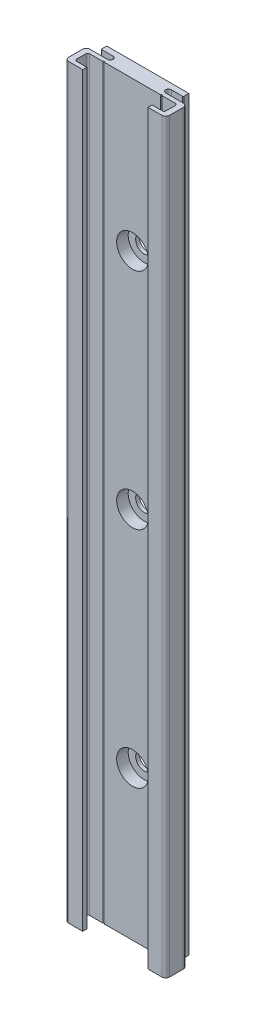
SolidWorks part; units mm, degrees
ref_plane "Plan de face" through (0, 0, 0) normal (0, 0, 1) x (1, 0, 0)
ref_plane "Plan de dessus" through (0, 0, 0) normal (0, 1, 0) x (1, 0, 0)
ref_plane "Plan de droite" through (0, 0, 0) normal (1, 0, 0) x (0, 0, -1)
ref_plane "Plan1" through (0, -100, 0) normal (0, -1, 0) x (1, 0, 0)
sketch "Esquisse1" plane through (0, -100, 0) normal (0, -1, 0) x (1, 0, 0)
  line L0 (-11, 0) -> (11, 0)
  line L1 (11, 0) -> (11, 1.5)
  line L2 (11, 1.5) -> (7.8, 1.5)
  line L3 (7.8, 3) -> (13.5, 3)
  line L4 (13.5, 3) -> (13.5, 8.7)
  line L5 (13.5, 8.7) -> (-13.5, 8.7)
  line L6 (-13.5, 8.7) -> (-13.5, 3)
  line L7 (-13.5, 3) -> (-7.8, 3)
  line L8 (-7.8, 1.5) -> (-11, 1.5)
  line L9 (-11, 1.5) -> (-11, 0)
  arc A0 (7.8, 1.5) -> (7.8, 3) centre (7.8, 2.25) cw
  arc A1 (-7.8, 3) -> (-7.8, 1.5) centre (-7.8, 2.25) cw
extrude "Boss.-Extru.1" add sketch "Esquisse1" against normal blind 200
sketch "Esquisse2" plane through (0, 100, 0) normal (0, 1, 0) x (-1, 0, 0)
  line L0 (8.75, 8.7) -> (-8.75, 8.7)
  line L1 (-8.75, 8.7) -> (-8.75, 7.6)
  line L2 (-8.75, 7.6) -> (-12, 7.6)
  line L3 (-12, 7.6) -> (-12, 4.1)
  line L4 (-12, 4.1) -> (12, 4.1)
  line L5 (12, 4.1) -> (12, 7.6)
  line L6 (12, 7.6) -> (8.75, 7.6)
  line L7 (8.75, 7.6) -> (8.75, 8.7)
  dimension "D1" = 17.5
  dimension "D2" = 24
  dimension "D3" = 1.1
  dimension "D4" = 3.5
  dimension "D5" = 3.25
extrude "Enlèv. mat.-Extru.1" cut sketch "Esquisse2" against normal through all
hole_wizard "Diamètre du perçage Ø0.4 (0.4)1" positions "Esquisse4" profile "Esquisse3" hole size "Ø0.4" standard "Ansi Metric"
sketch "Esquisse4" plane through (0, -100, 0) normal (0, -1, 0) x (-1, 0, 0)
  point P0 (-7.75, -4.1)
  point P1 (7.75, -4.1)
sketch "Esquisse3" plane through (7.75, -100, 4.1) normal (1, 0, 0) x (0, 0, -1)
  line L0 (0, 0) -> (0, 200)
  line L1 (0, 200) -> (0.2, 200)
  line L2 (0.2, 200) -> (0.2, 0)
  line L5 (0.2, 0) -> (0, 0)
  line L11 (0, -6.35) -> (0, 107.95) construction
  dimension "Diamètre du perçage jusqu'au prochain" = 0.4
  dimension "Profondeur du perçage jusqu'au prochain" = 200
hole_wizard "Chambrage pour vis à tête hexagonale M41" positions "Esquisse6" profile "Esquisse5" counterbore size "M4" standard "Ansi Metric" end condition through all
sketch "Esquisse6" plane through (0, 0, 4.1) normal (0, 0, 1) x (1, 0, 0)
  point P0 (0, -60)
  point P1 (0, 0)
  point P2 (0, 60)
  dimension "D1" = 60
  dimension "D2" = 60
sketch "Esquisse5" plane through (0, -60, 4.1) normal (1, 0, 0) x (0, -1, 0)
  line L0 (0, 0) -> (0, 4.1)
  line L1 (0, 4.1) -> (2.25, 4.1)
  line L3 (2.25, 4.1) -> (2.25, 3.1)
  line L4 (2.25, 3.1) -> (4.25, 3.1)
  line L5 (4.25, 3.1) -> (4.25, 0)
  line L7 (4.25, 0) -> (0, 0)
  line L11 (0, -6.35) -> (0, 107.95) construction
  dimension "Diamètre du perçage jusqu'au prochain" = 4.5
  dimension "Profondeur du perçage jusqu'au prochain" = 4.1
  dimension "Diamètre du chambrage" = 8.5
  dimension "Profondeur du chambrage" = 3.1
fillet "Congé1" radius 0.2 2 edges at (-11, 0, 1.5) (11, 0, 1.5)
fillet "Congé2" radius 0.5 4 edges at (12, 0, 7.6) (12, 0, 4.1) (-12, 0, 4.1) (-12, 0, 7.6)
fillet "Congé3" radius 1 4 edges at (13.5, 0, 8.7) (-13.5, 0, 3) (-13.5, 0, 8.7) (13.5, 0, 3)
